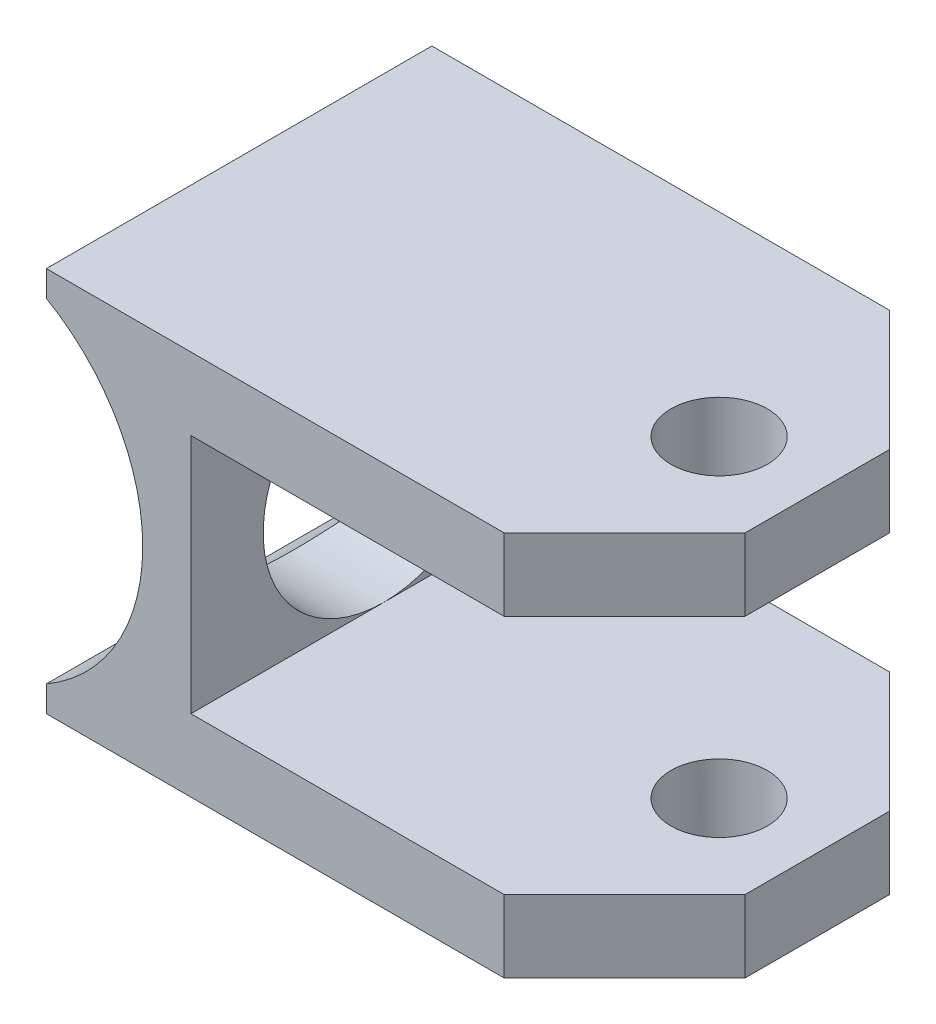
SolidWorks part; units mm, degrees
ref_plane "Front" through (0, 0, 0) normal (0, 0, 1) x (1, 0, 0)
ref_plane "Top" through (0, 0, 0) normal (0, 1, 0) x (1, 0, 0)
ref_plane "Right" through (0, 0, 0) normal (1, 0, 0) x (0, 0, -1)
sketch "Sketch1" plane through (0, 0, 0) normal (0, 0, 1) x (1, 0, 0)
  line L0 (6.35, 12.7) -> (44.45, 12.7)
  line L1 (44.45, 12.7) -> (44.45, 7.9375)
  line L2 (44.45, 7.9375) -> (15.875, 7.9375)
  line L3 (15.875, 7.9375) -> (15.875, -7.9375)
  line L4 (0, 0) -> (44.45, 0) construction
  line L5 (38.1, 12.7) -> (38.1, 0) construction
  line L6 (6.35, 12.7) -> (6.35, 10.9985)
  line L7 (44.45, -7.9375) -> (15.875, -7.9375)
  line L8 (44.45, -12.7) -> (44.45, -7.9375)
  line L9 (6.35, -12.7) -> (44.45, -12.7)
  line L10 (6.35, -12.7) -> (6.35, -10.9985)
  arc A0 (6.35, -10.9985) -> (6.35, 10.9985) centre (0, 0) ccw
  point P5 (12.7, 0)
  point P12 (15.875, 0)
  dimension "D1" = 25.4
  dimension "D2" = 7.9375
  dimension "D3" = 38.1
  dimension "D4" = 3.175
  dimension "D5" = 6.35
  dimension "D6" = 6.35
extrude "Boss-Extrude1" add sketch "Sketch1" along normal blind 25.4
hole_wizard "1/4 (0.25) Diameter Hole1" positions "Sketch2" profile "Sketch4" hole size "1/4" standard "ANSI Inch" end condition through all
sketch "Sketch2" plane through (0, 12.7, 0) normal (0, 1, 0) x (1, 0, 0)
  point P0 (38.1, -12.8218)
sketch "Sketch4" plane through (38.1, 12.7, 12.8218) normal (1, 0, 0) x (0, 0, 1)
  line L0 (0, 0) -> (0, 25.4)
  line L1 (0, 25.4) -> (3.175, 25.4)
  line L2 (3.175, 25.4) -> (3.175, 0)
  line L5 (3.175, 0) -> (0, 0)
  line L11 (0, -6.35) -> (0, 107.95) construction
  dimension "Thru Hole Dia." = 6.35
  dimension "Thru Hole Depth" = 25.4
chamfer "Chamfer1" distance 7.9375 angle 45 4 edges at (44.45, 10.3187, 0) (44.45, -10.3187, 0) (44.45, -10.3187, 25.4) (44.45, 10.3187, 25.4)
sketch3d "3DSketch1"
  line L0 (38.1, 12.7, 12.8218) -> (38.1, -12.7, 12.8218)
  line L1 (38.1, 0, 12.8218) -> (0, 0, 12.8218)
  circle A0 centre (38.1, 12.7, 12.8218) radius 3.175 construction
  circle A1 centre (38.1, -12.7, 12.8218) radius 3.175 construction
  point P3 (38.1, 0, 12.8218)
  point P6 (38.1, 15.875, 12.8218)
  point P9 (38.1, -9.525, 12.8218)
sketch "Sketch6" plane through (15.875, 0, 0) normal (1, 0, 0) x (0, 0, -1)
  line L0 (-25.4, 0) -> (0, 0) construction
  line L1 (-25.4, -7.9375) -> (-25.4, 7.9375) construction
  circle A0 centre (-12.7, 0) radius 7.9375
  dimension "D1" = 15.875
extrude "Cut-Extrude1" cut sketch "Sketch6" against normal through all
move or copy body "Body-Move/Copy1" [suppressed] bodies to move or copy 104
move or copy body "Body-Move/Copy2" [suppressed] bodies to move or copy 104
equation "\"D2@Sketch1\"=(.375)/2+.125"
